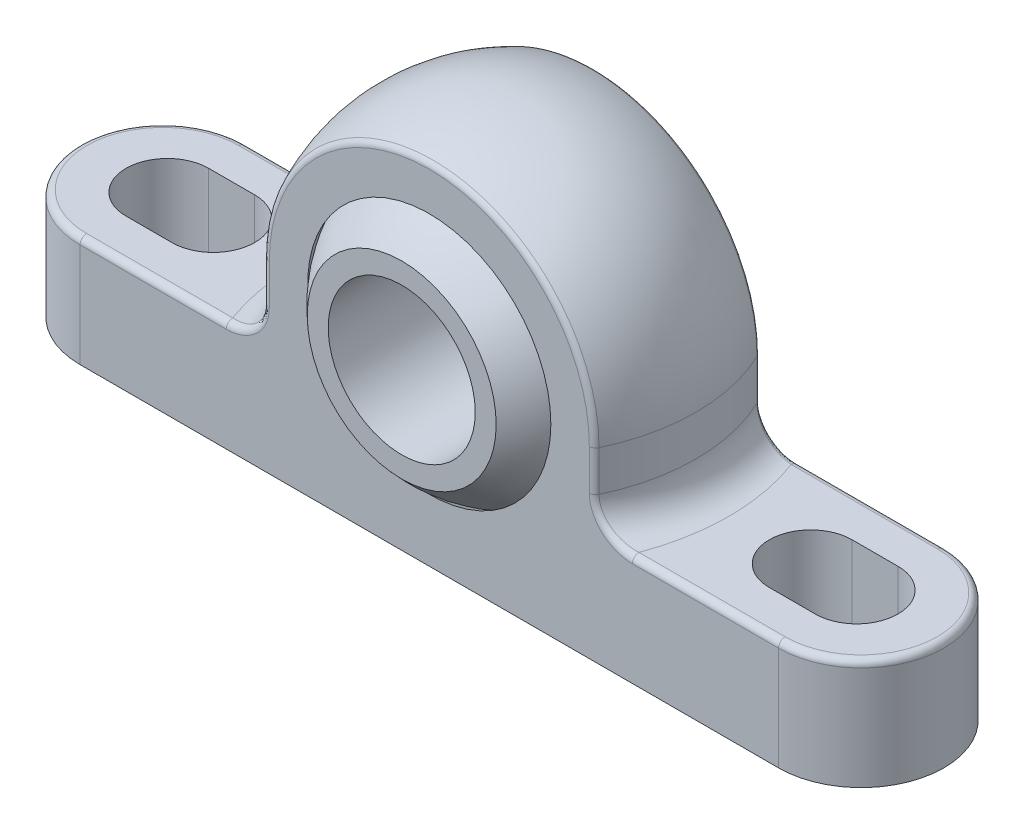
SolidWorks part; units mm, degrees
ref_plane "Front" through (0, 0, 0) normal (0, 0, 1) x (1, 0, 0)
ref_plane "Top" through (0, 0, 0) normal (0, 1, 0) x (1, 0, 0)
ref_plane "Right" through (0, 0, 0) normal (1, 0, 0) x (0, 0, -1)
sketch "Sketch1" plane through (0, 0, 0) normal (0, 0, 1) x (1, 0, 0)
  line L0 (-23.5, 0) -> (23.5, 0)
  line L1 (23.5, 0) -> (23.5, 6)
  line L2 (23.5, 6) -> (10, 6)
  line L3 (10, 6) -> (10, 10)
  line L4 (-10, 10) -> (-10, 6)
  line L5 (-10, 6) -> (-23.5, 6)
  line L6 (-23.5, 6) -> (-23.5, 0)
  line L7 (0, 0) -> (0, 10) construction
  arc A0 (10, 10) -> (-10, 10) centre (0, 10) ccw
  dimension "h3" = 6
  dimension "h1" = 10
  dimension "h2" = 20
  dimension "a" = 47
extrude "Extrude1" add sketch "Sketch1" along normal mid plane 9
sketch "Sketch2" plane through (0, 0, 0) normal (0, 0, 1) x (1, 0, 0)
  line L0 (10, 10) -> (15, 10) construction
  line L1 (15, 6) -> (15, 25)
  line L2 (15, 25) -> (0, 25)
  line L3 (0, 25) -> (0, 20)
  line L4 (0, 25) -> (0, 30) construction
  line L9 (23.5, 6) -> (10, 6) construction
  line L10 (10, 6) -> (10, 10) construction
  line L13 (15, 6) -> (10, 6)
  line L14 (10, 6) -> (10, 10)
  arc A0 (10, 10) -> (-10, 10) centre (0, 10) ccw construction
  arc A1 (10, 10) -> (0, 20) centre (0, 10) ccw
  dimension "D1" = 5
revolve "Cut-Revolve1" cut sketch "Sketch2" angle 360 about L4
sketch "Sketch3" plane through (0, 0, 0) normal (0, 1, 0) x (1, 0, 0)
  line L0 (-19, 4.5) -> (19, 4.5)
  line L1 (-19, -4.5) -> (19, -4.5)
  line L2 (-23.5, -4.5) -> (23.5, -4.5) construction
  line L5 (-23.5, 4.5) -> (23.5, 4.5) construction
  line L6 (-18.75, 0) -> (-16.25, 0) construction
  line L7 (-16.25, 0) -> (16.25, 0) construction
  line L8 (16.25, 0) -> (18.75, 0) construction
  line L9 (-18.75, 2.25) -> (-16.25, 2.25)
  line L10 (16.25, 2.25) -> (18.75, 2.25)
  line L11 (18.75, -2.25) -> (16.25, -2.25)
  line L12 (-16.25, -2.25) -> (-18.75, -2.25)
  arc A0 (19, 4.5) -> (19, -4.5) centre (19, 0) cw
  arc A1 (-19, 4.5) -> (-19, -4.5) centre (-19, 0) ccw
  arc A2 (18.75, 2.25) -> (18.75, -2.25) centre (18.75, 0) cw
  arc A3 (16.25, 2.25) -> (16.25, -2.25) centre (16.25, 0) ccw
  arc A4 (-16.25, 2.25) -> (-16.25, -2.25) centre (-16.25, 0) cw
  arc A5 (-18.75, 2.25) -> (-18.75, -2.25) centre (-18.75, 0) ccw
  point P24 (17.5, 0)
  point P25 (-17.5, 0)
  dimension "D1" = 35
  dimension "X2" = 7
  dimension "d3" = 4.5
extrude "Cut-Extrude1" cut sketch "Sketch3" along normal through all flip side to cut
sketch "Sketch4" plane through (0, 0, 0) normal (0, 0, 1) x (1, 0, 0)
  line L0 (0, 2) -> (0, 18)
  line L1 (0, 2) -> (0, 0) construction
  arc A0 (0, 18) -> (0, 2) centre (0, 10) cw
  arc A1 (10, 10) -> (0, 20) centre (0, 10) ccw construction
  arc A2 (10, 10) -> (0, 20) centre (0, 10) ccw construction
  dimension "D1" = 20
  dimension "D2" = 16
revolve "Cut-Revolve2" cut sketch "Sketch4" angle 360 about L1
sketch "Sketch5" plane through (0, 0, 0) normal (0, 0, 1) x (1, 0, 0)
  line L0 (0, 2.1) -> (0, 17.9)
  line L1 (0, 2) -> (0, 18) construction
  line L2 (0, 2.1) -> (0, 0) construction
  arc A0 (0, 17.9) -> (0, 2.1) centre (0, 10) cw
  dimension "D1" = 0.1
revolve "Revolve1" add sketch "Sketch5" angle 360 about L2
sketch "Sketch6" plane through (0, 0, 0) normal (1, 0, 0) x (0, 0, -1)
  line L1 (-6, 25) -> (6, 25)
  line L2 (-6, 25) -> (-6, 0)
  line L3 (-6, 0) -> (6, 0)
  line L4 (6, 25) -> (6, 0)
  dimension "B" = 12
extrude "Cut-Extrude2" cut sketch "Sketch6" against normal through all and the other way through all flip side to cut
sketch "Sketch7" plane through (0, 0, 0) normal (0, 0, 1) x (1, 0, 0)
  circle A0 centre (0, 10) radius 4
  dimension "Shaft Dia" = 8
extrude "Cut-Extrude3" cut sketch "Sketch7" against normal through all and the other way through all
fillet "Fillet2" radius 1.8 2 edges at (10, 6, 0) (-10, 6, 0)
fillet "Fillet1" radius 0.36 16 edges at (-14.9541, 6, -4.5) (-23.5, 6, 0) (14.9541, 6, -4.5) (23.5, 6, 0) (-14.9541, 6, 4.5) (14.9541, 6, 4.5) (9.2984, 6.7611, -4.5) (8.9303, 8.9, -4.5) (0, 18.9303, -4.5) (-8.9303, 8.9, -4.5) (-9.5905, 6.464, -4.5) (-9.2984, 6.7611, 4.5) (-8.9303, 8.9, 4.5) (0, 18.9303, 4.5) (8.9303, 8.9, 4.5) (9.5905, 6.464, 4.5)
sketch "Sketch8" plane through (0, 0, 0) normal (1, 0, 0) x (0, 0, -1)
  line L0 (0, 10) -> (-6, 11.3302) construction
  line L1 (0, 2.1) -> (0, 17.9) construction
  line L2 (0, 10) -> (-6, 8.6698) construction
  line L3 (-6, 25) -> (-6, 0) construction
  line L4 (-6, 0) -> (6, 0) construction
  dimension "Max Misalignmnet" = 25
  dimension "D2" = 12.5
equation "\"D2@Sketch4\"=\"D1@Sketch4\"*.8"
equation "\"D1@Fillet2\"=\"C1@Extrude1\"/5"
equation "\"D1@Fillet1\"=\"C1@Extrude1\"/25"
equation "\"D2@Sketch8\"=\"Max Misalignmnet@Sketch8\" /2"
